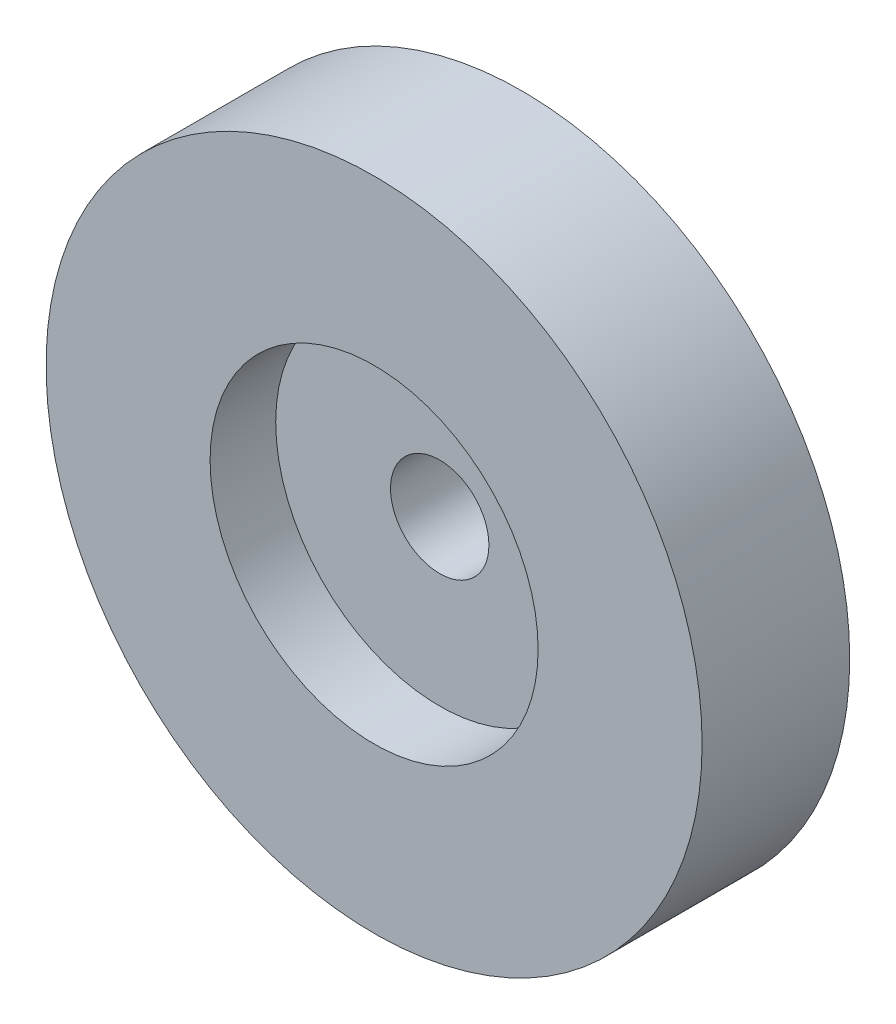
SolidWorks part; units mm, degrees
ref_plane "Plan de face" through (0, 0, 0) normal (0, 0, 1) x (1, 0, 0)
ref_plane "Plan de dessus" through (0, 0, 0) normal (0, 1, 0) x (1, 0, 0)
ref_plane "Plan de droite" through (0, 0, 0) normal (1, 0, 0) x (0, 0, -1)
sketch "Esquisse2" plane through (0, 0, 0) normal (0, 1, 0) x (1, 0, 0)
  line L1 (0, 0) -> (40, 0)
  line L2 (0, 0) -> (0, 18)
  line L3 (0, 18) -> (40, 18)
  line L4 (40, 0) -> (40, 18)
  line L5 (0, 0) -> (20, 0)
  line L6 (0, 0) -> (0, 8)
  line L7 (0, 8) -> (20, 8)
  line L8 (20, 0) -> (20, 8)
  line L9 (0, 0) -> (6, 0)
  line L10 (0, 0) -> (0, 18)
  line L11 (0, 18) -> (6, 18)
  line L12 (6, 0) -> (6, 18)
  dimension "D1" = 20
  dimension "D2" = 8
  dimension "D3" = 18
  dimension "D4" = 40
  dimension "D5" = 6
revolve "Révolution1" add sketch "Esquisse2" angle 360 about L2
